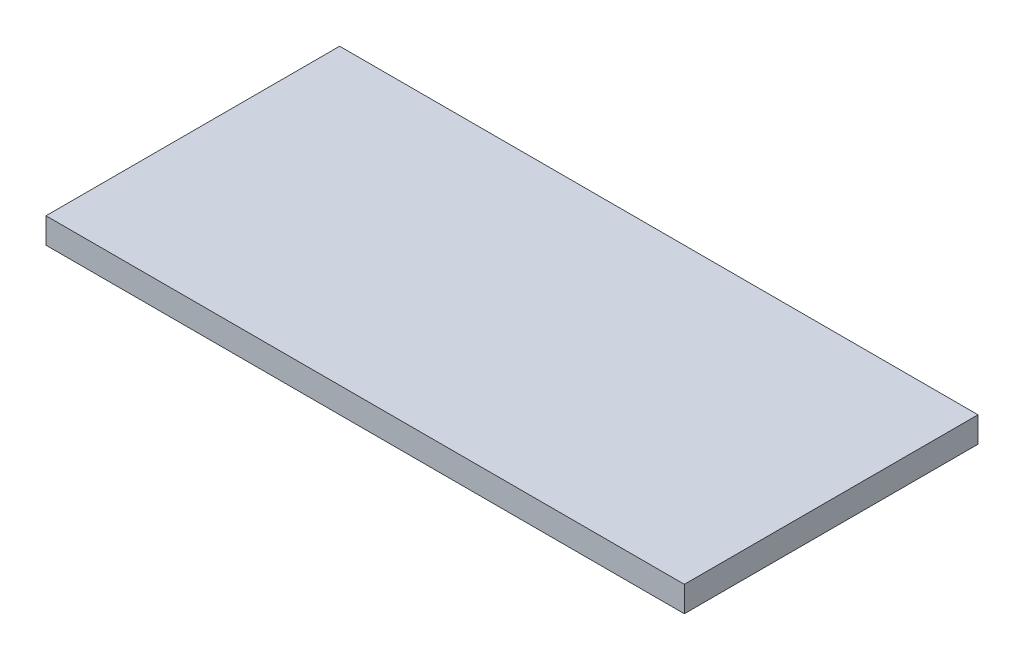
SolidWorks part; units mm, degrees
ref_plane "Front Plane" through (0, 0, 0) normal (0, 0, 1) x (1, 0, 0)
ref_plane "Top Plane" through (0, 0, 0) normal (0, 1, 0) x (1, 0, 0)
ref_plane "Right Plane" through (0, 0, 0) normal (1, 0, 0) x (0, 0, -1)
sketch "Sketch1" plane through (0, 0, 0) normal (0, 1, 0) x (1, 0, 0)
  line L1 (-75, -34.5) -> (75, -34.5)
  line L2 (-75, -34.5) -> (-75, 34.5)
  line L3 (-75, 34.5) -> (75, 34.5)
  line L4 (75, -34.5) -> (75, 34.5)
  line L5 (-75, -34.5) -> (75, 34.5) construction
  line L6 (-75, 34.5) -> (75, -34.5) construction
  point P0 (0, 0)
  dimension "D1" = 69
  dimension "D2" = 150
extrude "Boss-Extrude1" add sketch "Sketch1" along normal blind 6
